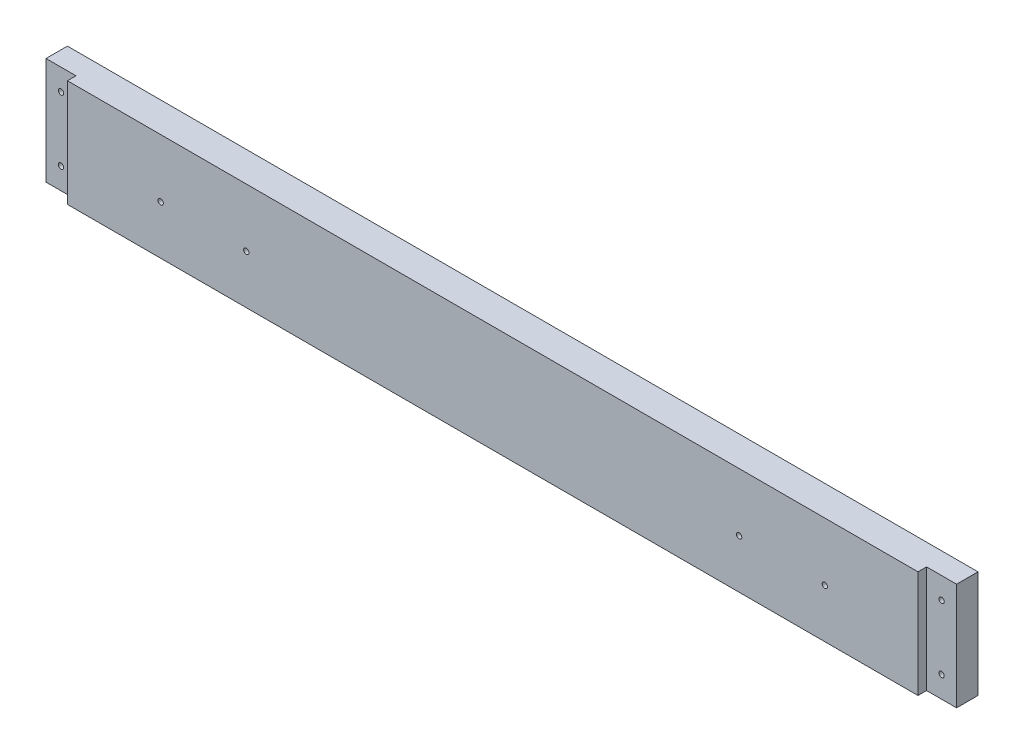
SolidWorks part; units mm, degrees
material "Pine"
ref_plane "Front Plane" through (0, 0, 0) normal (0, 0, 1) x (1, 0, 0)
ref_plane "Top Plane" through (0, 0, 0) normal (0, 1, 0) x (1, 0, 0)
ref_plane "Right Plane" through (0, 0, 0) normal (1, 0, 0) x (0, 0, -1)
sketch "Sketch1" plane through (0, 0, 0) normal (0, 0, 1) x (1, 0, 0)
  line L0 (8932.6508, -5243.5125) -> (10226.1458, -5243.5125)
  line L1 (9086.3208, -4722.0918) -> (10222.9708, -4853.7812)
  line L2 (8914.8708, -6342.0625) -> (10197.5708, -6342.0625)
  line L3 (8914.8708, -5808.6625) -> (10197.5708, -5808.6625)
  line L4 (8919.6333, -5253.0375) -> (10218.2083, -5253.0375)
  line L5 (9134.2633, -4656.1375) -> (9134.2633, -4638.3575)
  line L6 (9091.0833, -4638.3575) -> (9134.2633, -4638.3575)
  line L7 (9091.0833, -4567.2375) -> (9091.0833, -4638.3575)
  line L8 (9134.2633, -4656.1375) -> (9581.3033, -4656.1375)
  line L9 (9091.0833, -4567.2375) -> (9624.4833, -4567.2375)
  line L10 (9581.3033, -4656.1375) -> (9581.3033, -4638.3575)
  line L11 (9581.3033, -4638.3575) -> (9624.4833, -4638.3575)
  line L12 (9624.4833, -4567.2375) -> (9624.4833, -4638.3575)
  line L13 (8932.6508, -5225.7325) -> (9344.9775, -5225.7325)
  line L14 (8932.6508, -5256.2125) -> (8932.6508, -5243.5125)
  line L15 (8911.6958, -5256.2125) -> (8932.6508, -5256.2125)
  line L16 (8914.8708, -4722.0918) -> (9086.3208, -4722.0918)
  line L17 (8911.6958, -4715.5913) -> (8932.6508, -4715.5913)
  line L18 (8914.8708, -6342.0625) -> (8914.8708, -5808.6625)
  line L19 (12082.9917, -4722.0918) -> (10946.3417, -4853.7812)
  line L20 (12236.6617, -5243.5125) -> (10943.1667, -5243.5125)
  line L21 (10951.1042, -5253.0375) -> (12249.6792, -5253.0375)
  line L22 (10838.3917, -5656.2625) -> (11308.2917, -5656.2625)
  line L23 (10838.3917, -5719.7625) -> (11308.2917, -5719.7625)
  line L24 (10838.3917, -5742.5368) -> (11308.2917, -5742.5368)
  line L25 (10806.6417, -6342.0625) -> (11340.0417, -6342.0625)
  line L26 (10803.4667, -6335.7125) -> (11343.2167, -6335.7125)
  line L27 (10803.4667, -6317.9325) -> (11343.2167, -6317.9325)
  line L28 (10943.1667, -5225.7325) -> (11376.4483, -5225.7325)
  line L29 (11506.7292, -4754.5625) -> (10806.6417, -4827.5875)
  line L30 (11506.7292, -4567.2375) -> (11506.7292, -4754.5625)
  line L31 (10806.6417, -4567.2375) -> (10806.6417, -4827.5875)
  line L32 (10806.6417, -4567.2375) -> (11506.7292, -4567.2375)
  line L33 (10235.6708, -6329.3625) -> (10245.1958, -6329.3625)
  line L34 (10245.1958, -6329.3625) -> (10254.7208, -6278.5625)
  line L35 (10302.3458, -6329.3625) -> (10311.8708, -6278.5625)
  line L36 (10302.3458, -6329.3625) -> (10292.8208, -6329.3625)
  line L37 (10245.1958, -5821.3625) -> (10254.7208, -5872.1625)
  line L38 (10235.6708, -5821.3625) -> (10245.1958, -5821.3625)
  line L39 (10292.8208, -5821.3625) -> (10302.3458, -5821.3625)
  line L40 (10302.3458, -5821.3625) -> (10311.8708, -5872.1625)
  line L41 (10235.6708, -5821.3625) -> (10235.6708, -6329.3625)
  line L42 (10254.7208, -5872.1625) -> (10254.7208, -6278.5625)
  line L43 (10311.8708, -5872.1625) -> (10311.8708, -6278.5625)
  line L44 (10292.8208, -5821.3625) -> (10292.8208, -6329.3625)
  line L45 (8932.6508, -5225.7325) -> (8932.6508, -4715.5913)
  line L46 (8911.6958, -4715.5913) -> (8911.6958, -5256.2125)
  line L47 (8914.8708, -5248.275) -> (8914.8708, -4722.0918)
  line L48 (8919.6333, -5253.0375) -> (8914.8708, -5248.275)
  line L49 (8914.8708, -5145.0875) -> (8937.426, -5145.0875)
  line L50 (8914.8708, -5202.2375) -> (8937.426, -5202.2375)
  line L51 (10838.3917, -5656.2625) -> (10838.3917, -5719.7625)
  line L52 (10832.0417, -5736.1868) -> (10856.1717, -5736.1868)
  line L53 (10806.6417, -6342.0625) -> (10806.6417, -5818.7368)
  line L54 (10832.0417, -5649.9125) -> (10856.1717, -5649.9125)
  line L55 (10832.0417, -5726.1125) -> (10856.1717, -5726.1125)
  line L56 (10806.6417, -5818.7368) -> (10833.9015, -5818.7368)
  line L57 (10832.0417, -5806.0442) -> (10851.6815, -5806.0442)
  line L58 (10856.1717, -5801.5541) -> (10856.1717, -5736.1868)
  line L59 (10838.3917, -5814.2467) -> (10838.3917, -5742.5368)
  line L60 (10832.0417, -5806.0442) -> (10832.0417, -5736.1868)
  line L61 (10803.4667, -6317.9325) -> (10803.4667, -6335.7125)
  line L62 (10197.5708, -5808.6625) -> (10197.5708, -6342.0625)
  line L63 (9762.3842, -6348.4125) -> (9762.3842, -5802.3125)
  line L64 (9780.1642, -6348.4125) -> (9762.3842, -6348.4125)
  line L65 (9780.1642, -5802.3125) -> (9780.1642, -6348.4125)
  line L66 (9762.3842, -5802.3125) -> (9780.1642, -5802.3125)
  line L67 (9332.2775, -6348.4125) -> (9332.2775, -5802.3125)
  line L68 (9332.2775, -6348.4125) -> (9350.0575, -6348.4125)
  line L69 (9350.0575, -5802.3125) -> (9350.0575, -6348.4125)
  line L70 (9332.2775, -5802.3125) -> (9350.0575, -5802.3125)
  line L71 (9993.8374, -6061.075) -> (9993.8374, -6045.2418)
  line L72 (9998.5999, -6065.8375) -> (10014.4331, -6065.8375)
  line L73 (9998.5999, -6084.8875) -> (10014.4331, -6084.8875)
  line L74 (9993.8374, -6105.4832) -> (9993.8374, -6089.65)
  line L75 (9974.7874, -6105.4832) -> (9974.7874, -6089.65)
  line L76 (9954.1917, -6084.8875) -> (9970.0249, -6084.8875)
  line L77 (9974.7874, -6061.075) -> (9974.7874, -6045.2418)
  line L78 (9954.1917, -6065.8375) -> (9970.0249, -6065.8375)
  line L79 (10793.9417, -6237.2875) -> (10816.4969, -6237.2875)
  line L80 (10793.9417, -6294.4375) -> (10816.4969, -6294.4375)
  line L81 (10856.1717, -5649.9125) -> (10856.1717, -5726.1125)
  line L82 (10832.0417, -5726.1125) -> (10832.0417, -5649.9125)
  line L83 (10226.1458, -5225.7325) -> (10226.1458, -5243.5125)
  line L84 (10205.1908, -5257.8) -> (10205.1908, -4844.2499)
  line L85 (10230.9083, -4844.2499) -> (10230.9083, -5257.8)
  line L86 (10205.1908, -5257.8) -> (10230.9083, -5257.8)
  line L87 (10205.1908, -4844.2499) -> (10230.9083, -4844.2499)
  line L88 (10946.3417, -5176.8375) -> (10968.8969, -5176.8375)
  line L89 (9349.4676, -5141.9125) -> (9358.2674, -5141.9125)
  line L90 (10946.3417, -5119.6875) -> (10968.8969, -5119.6875)
  line L91 (9929.011, -4660.9635) -> (10066.0807, -4660.9635)
  line L92 (9929.011, -4678.7435) -> (10066.0807, -4678.7435)
  line L93 (10943.1667, -5225.7325) -> (10943.1667, -5243.5125)
  line L94 (10946.3417, -5248.275) -> (10951.1042, -5253.0375)
  line L95 (10946.3417, -5257.8063) -> (10946.3417, -4849.0188)
  line L96 (10964.1217, -5257.8) -> (10964.1217, -4844.2499)
  line L97 (10938.4042, -4844.2499) -> (10938.4042, -5257.8)
  line L98 (10938.4042, -5257.8) -> (10964.1217, -5257.8)
  line L99 (10964.1217, -4844.2499) -> (10938.4042, -4844.2499)
  line L100 (10344.8908, -4560.8875) -> (10369.0208, -4560.8875)
  line L101 (10344.8908, -4560.8875) -> (10369.0208, -4560.8875)
  line L102 (10800.2917, -4560.8875) -> (10824.4217, -4560.8875)
  line L103 (10200.4156, -5119.6875) -> (10222.9708, -5119.6875)
  line L104 (10200.4156, -5176.8375) -> (10222.9708, -5176.8375)
  line L105 (9344.9775, -5146.4026) -> (9344.9775, -5225.7325)
  line L106 (10344.8908, -4560.8875) -> (10344.8908, -4833.9375)
  line L107 (9792.8642, -5225.7325) -> (9792.8642, -5146.4026)
  line L108 (9362.7575, -5225.7325) -> (9775.0842, -5225.7325)
  line L109 (9680.3633, -4761.8396) -> (9680.3633, -4559.9604)
  line L110 (9656.2333, -4559.9604) -> (9680.3633, -4559.9604)
  line L111 (9656.2333, -4761.8396) -> (9680.3633, -4761.8396)
  line L112 (9656.2333, -4761.8396) -> (9656.2333, -4559.9604)
  line L113 (9779.5743, -5141.9125) -> (9788.374, -5141.9125)
  line L114 (10070.5708, -4665.4536) -> (10070.5708, -4674.2534)
  line L115 (9924.5208, -4674.2534) -> (9924.5208, -4665.4536)
  line L116 (12127.4417, -6188.3925) -> (12205.5015, -6188.3925)
  line L117 (12209.9917, -6170.6125) -> (12209.9917, -6183.9024)
  line L118 (9792.8642, -5225.7325) -> (10226.1458, -5225.7325)
  line L119 (9662.5833, -4754.5625) -> (10362.6708, -4827.5875)
  line L120 (9662.5833, -4567.2375) -> (9662.5833, -4754.5625)
  line L121 (10362.6708, -4567.2375) -> (10362.6708, -4827.5875)
  line L122 (9662.5833, -4567.2375) -> (10362.6708, -4567.2375)
  line L123 (10824.4217, -4833.9375) -> (10800.2917, -4833.9375)
  line L124 (10800.2917, -4833.9375) -> (10800.2917, -4560.8875)
  line L125 (10824.4217, -4560.8875) -> (10824.4217, -4833.9375)
  line L126 (10344.8908, -4833.9375) -> (10369.0208, -4833.9375)
  line L127 (10369.0208, -4833.9375) -> (10369.0208, -4560.8875)
  line L128 (10222.9708, -5248.275) -> (10218.2083, -5253.0375)
  line L129 (10222.9708, -5257.8063) -> (10222.9708, -4849.0188)
  line L130 (11734.6544, -5701.375) -> (11739.2301, -5701.375)
  line L131 (9362.7575, -5225.7325) -> (9362.7575, -5146.4026)
  line L132 (9775.0842, -5146.4026) -> (9775.0842, -5225.7325)
  line L133 (11761.3864, -5701.375) -> (11756.8282, -5701.375)
  line L134 (11734.6544, -5693.755) -> (11739.2301, -5693.755)
  line L135 (11761.4039, -5693.755) -> (11756.8282, -5693.755)
  line L136 (11734.6544, -5701.375) -> (11739.2301, -5701.375)
  line L137 (11744.3462, -5721.3024) -> (11744.3462, -5706.4179)
  line L138 (11751.7122, -5721.3024) -> (11751.7122, -5706.4179)
  line L139 (11740.0917, -6170.6125) -> (11740.0917, -6183.9024)
  line L140 (11689.2917, -6188.3925) -> (11822.6417, -6188.3925)
  line L141 (11689.2917, -6348.4093) -> (11689.2917, -6164.2657)
  line L142 (11689.2917, -6164.2657) -> (11746.4417, -6164.2657)
  line L143 (11746.4417, -6164.2657) -> (11746.4417, -6188.3925)
  line L144 (11689.2917, -6164.2657) -> (11746.4417, -6164.2657)
  line L145 (11340.0417, -5818.7368) -> (11340.0417, -6342.0625)
  line L146 (11290.5117, -5726.1125) -> (11314.6417, -5726.1125)
  line L147 (11290.5117, -5649.9125) -> (11290.5117, -5726.1125)
  line L148 (11340.0417, -5818.7368) -> (11312.7818, -5818.7368)
  line L149 (11314.6417, -5806.0442) -> (11295.0018, -5806.0442)
  line L150 (11290.5117, -5801.5541) -> (11290.5117, -5736.1868)
  line L151 (11308.2917, -5814.2467) -> (11308.2917, -5742.5368)
  line L152 (11314.6417, -5806.0442) -> (11314.6417, -5736.1868)
  line L153 (11290.5117, -5736.1868) -> (11314.6417, -5736.1868)
  line L154 (11848.0417, -6267.1325) -> (11962.3417, -6267.1325)
  line L155 (11962.3417, -6267.1325) -> (11962.3417, -6203.6325)
  line L156 (11343.2167, -6317.9325) -> (11343.2167, -6335.7125)
  line L157 (11365.4417, -5656.2625) -> (11365.4417, -5719.7625)
  line L158 (11365.4417, -5656.2625) -> (11479.7417, -5656.2625)
  line L159 (11778.1917, -6071.3937) -> (11802.3217, -6071.3937)
  line L160 (11314.6417, -5726.1125) -> (11314.6417, -5649.9125)
  line L161 (11314.6417, -5649.9125) -> (11290.5117, -5649.9125)
  line L162 (11308.2917, -5719.7625) -> (11308.2917, -5656.2625)
  line L163 (11689.2917, -6348.4093) -> (11713.4217, -6348.4093)
  line L164 (12203.6417, -6164.2657) -> (12260.7917, -6164.2657)
  line L165 (11713.4217, -6348.4093) -> (11713.4217, -6164.2657)
  line L166 (11695.6417, -6342.0625) -> (11695.6417, -6170.6125)
  line L167 (11695.6417, -6048.5337) -> (11699.4517, -6052.3437)
  line L168 (11822.6417, -6292.5325) -> (11822.6417, -6188.3925)
  line L169 (11695.6417, -6342.0625) -> (11695.6417, -6170.6125)
  line L170 (11848.0417, -6203.6325) -> (11962.3417, -6203.6325)
  line L171 (11848.0417, -6203.6325) -> (11848.0417, -6267.1325)
  line L172 (11987.7417, -6267.1325) -> (11987.7417, -6203.6325)
  line L173 (11784.5417, -6077.7437) -> (11784.5417, -6141.2438)
  line L174 (11517.8417, -5656.2625) -> (11632.1417, -5656.2625)
  line L175 (11632.1417, -5656.2625) -> (11632.1417, -5719.7625)
  line L176 (11632.1417, -5719.7625) -> (11517.8417, -5719.7625)
  line L177 (11517.8417, -5719.7625) -> (11517.8417, -5656.2625)
  line L178 (11692.4667, -6028.2137) -> (11692.4667, -6045.9937)
  line L179 (11695.6417, -5979.3188) -> (11718.1969, -5979.3188)
  line L180 (11695.6417, -5922.1687) -> (11718.1969, -5922.1687)
  line L181 (11821.0415, -5722.9375) -> (11821.0415, -5943.6)
  line L182 (11687.7042, -5651.5) -> (11701.9917, -5651.5)
  line L183 (11687.7042, -5651.5) -> (11687.7042, -6055.5251)
  line L184 (11687.7042, -6055.5251) -> (11701.9917, -6055.5251)
  line L185 (11701.9917, -6055.5251) -> (11701.9917, -5651.5)
  line L186 (11695.6417, -6055.2013) -> (11695.6417, -5649.595)
  line L187 (11695.6417, -5656.2625) -> (11695.6417, -6048.5337)
  line L188 (11695.6417, -6170.6125) -> (11740.0917, -6170.6125)
  line L189 (12203.6417, -6164.2657) -> (12203.6417, -6188.3925)
  line L190 (12254.4417, -6342.0625) -> (12254.4417, -6170.6125)
  line L191 (12129.0419, -5943.6) -> (12129.0419, -5722.9375)
  line L192 (12254.4417, -6048.5337) -> (12250.6317, -6052.3437)
  line L193 (12257.6167, -6045.9937) -> (12257.6167, -6028.2137)
  line L194 (12248.0917, -5651.5) -> (12262.3792, -5651.5)
  line L195 (12262.3792, -5651.5) -> (12262.3792, -6055.5251)
  line L196 (12262.3792, -6055.5251) -> (12248.0917, -6055.5251)
  line L197 (12248.0917, -6055.5251) -> (12248.0917, -5651.5)
  line L198 (12254.4417, -6141.2438) -> (12254.4417, -6077.7437)
  line L199 (12236.6617, -6164.2657) -> (12260.7917, -6164.2657)
  line L200 (12102.0417, -6267.1325) -> (11987.7417, -6267.1325)
  line L201 (11330.1865, -6237.2875) -> (11352.7417, -6237.2875)
  line L202 (11330.1865, -6294.4375) -> (11352.7417, -6294.4375)
  line L203 (11474.6617, -5851.8425) -> (11492.4417, -5851.8425)
  line L204 (11474.6617, -5808.6625) -> (11474.6617, -5851.8425)
  line L205 (11403.5417, -5808.6625) -> (11474.6617, -5808.6625)
  line L206 (11492.4417, -5851.8425) -> (11492.4417, -6298.8825)
  line L207 (11403.5417, -6342.0625) -> (11403.5417, -5808.6625)
  line L208 (11474.6617, -6298.8825) -> (11492.4417, -6298.8825)
  line L209 (11474.6617, -6342.0625) -> (11474.6617, -6298.8825)
  line L210 (11403.5417, -6342.0625) -> (11474.6617, -6342.0625)
  line L211 (11619.4417, -5851.8425) -> (11601.6617, -5851.8425)
  line L212 (11601.6617, -5808.6625) -> (11601.6617, -5851.8425)
  line L213 (11530.5417, -5808.6625) -> (11601.6617, -5808.6625)
  line L214 (11619.4417, -5851.8425) -> (11619.4417, -6298.8825)
  line L215 (11530.5417, -6342.0625) -> (11530.5417, -5808.6625)
  line L216 (11619.4417, -6298.8825) -> (11601.6617, -6298.8825)
  line L217 (11601.6617, -6342.0625) -> (11601.6617, -6298.8825)
  line L218 (11530.5417, -6342.0625) -> (11601.6617, -6342.0625)
  line L219 (11479.7417, -5719.7625) -> (11479.7417, -5656.2625)
  line L220 (11365.4417, -5719.7625) -> (11479.7417, -5719.7625)
  line L221 (11778.1917, -6147.5937) -> (11802.3217, -6147.5937)
  line L222 (11802.3217, -6071.3937) -> (11802.3217, -6147.5937)
  line L223 (11778.1917, -6147.5937) -> (11778.1917, -6071.3937)
  line L224 (12254.4417, -5922.1687) -> (12231.8865, -5922.1687)
  line L225 (12254.4417, -5979.3188) -> (12231.8865, -5979.3188)
  line L226 (12254.4417, -6055.2013) -> (12254.4417, -5649.595)
  line L227 (12254.4417, -6048.5337) -> (12254.4417, -5656.2625)
  line L228 (11841.6917, -5702.2873) -> (12108.3917, -5702.2873)
  line L229 (11822.6417, -6292.5325) -> (12127.4417, -6292.5325)
  line L230 (12127.4417, -6292.5325) -> (12127.4417, -6188.3925)
  line L231 (12254.4417, -6170.6125) -> (12209.9917, -6170.6125)
  line L232 (11695.6417, -6342.0625) -> (12254.4417, -6342.0625)
  line L233 (12236.6617, -6348.4093) -> (12260.7917, -6348.4093)
  line L234 (12260.7917, -6348.4093) -> (12260.7917, -6164.2657)
  line L235 (12236.6617, -6348.4093) -> (12236.6617, -6164.2657)
  line L236 (12102.0417, -6203.6325) -> (12102.0417, -6267.1325)
  line L237 (11987.7417, -6203.6325) -> (12102.0417, -6203.6325)
  line L238 (12236.6617, -6147.5937) -> (12236.6617, -6071.3937)
  line L239 (12203.6417, -6188.3925) -> (12260.7917, -6188.3925)
  line L240 (11098.7417, -4665.4536) -> (11098.7417, -4674.2534)
  line L241 (11394.2283, -5146.4026) -> (11394.2283, -5225.7325)
  line L242 (11376.4483, -5225.7325) -> (11376.4483, -5146.4026)
  line L243 (11394.2283, -5225.7325) -> (11806.555, -5225.7325)
  line L244 (11841.6917, -5964.2502) -> (12108.3917, -5964.2502)
  line L245 (12236.6617, -6147.5937) -> (12260.7917, -6147.5937)
  line L246 (12236.6617, -5256.2125) -> (12236.6617, -5243.5125)
  line L247 (12260.7917, -6147.5937) -> (12260.7917, -6071.3937)
  line L248 (12260.7917, -6071.3937) -> (12236.6617, -6071.3937)
  line L249 (12254.4417, -6077.7437) -> (11784.5417, -6077.7437)
  line L250 (11784.5417, -6141.2438) -> (12254.4417, -6141.2438)
  line L252 (12254.4417, -5656.2625) -> (11695.6417, -5656.2625)
  line L253 (11699.4517, -6052.3437) -> (12250.6317, -6052.3437)
  line L254 (11692.4667, -6045.9937) -> (12257.6167, -6045.9937)
  line L255 (11692.4667, -6028.2137) -> (12257.6167, -6028.2137)
  line L256 (11824.335, -5146.4026) -> (11824.335, -5225.7325)
  line L257 (11811.0451, -5141.9125) -> (11819.8449, -5141.9125)
  line L258 (11244.7917, -4674.2534) -> (11244.7917, -4665.4536)
  line L259 (11806.555, -5225.7325) -> (11806.555, -5146.4026)
  line L260 (11488.9492, -4761.8396) -> (11488.9492, -4559.9604)
  line L261 (11488.9492, -4559.9604) -> (11513.0792, -4559.9604)
  line L262 (11488.9492, -4761.8396) -> (11513.0792, -4761.8396)
  line L263 (11513.0792, -4761.8396) -> (11513.0792, -4559.9604)
  line L264 (11240.3015, -4660.9635) -> (11103.2318, -4660.9635)
  line L265 (11103.2318, -4678.7435) -> (11240.3015, -4678.7435)
  line L266 (12236.6617, -5225.7325) -> (12236.6617, -4715.5913)
  line L267 (12257.6167, -4715.5913) -> (12257.6167, -5256.2125)
  line L268 (12254.4417, -5248.275) -> (12254.4417, -4722.0918)
  line L269 (12236.6617, -5225.7325) -> (11824.335, -5225.7325)
  line L270 (12035.0492, -4656.1375) -> (12035.0492, -4638.3575)
  line L271 (12078.2292, -4638.3575) -> (12035.0492, -4638.3575)
  line L272 (12078.2292, -4567.2375) -> (12078.2292, -4638.3575)
  line L273 (12035.0492, -4656.1375) -> (11588.0092, -4656.1375)
  line L274 (11544.8292, -4567.2375) -> (12078.2292, -4567.2375)
  line L275 (11588.0092, -4656.1375) -> (11588.0092, -4638.3575)
  line L276 (11544.8292, -4638.3575) -> (11588.0092, -4638.3575)
  line L277 (11544.8292, -4567.2375) -> (11544.8292, -4638.3575)
  line L278 (12249.6792, -5253.0375) -> (12254.4417, -5248.275)
  line L280 (12257.6167, -5256.2125) -> (12236.6617, -5256.2125)
  line L281 (12231.8865, -5145.0875) -> (12254.4417, -5145.0875)
  line L282 (12231.8865, -5202.2375) -> (12254.4417, -5202.2375)
  line L283 (12236.6617, -4715.5913) -> (12257.6167, -4715.5913)
  line L284 (12082.9917, -4722.0918) -> (12254.4417, -4722.0918)
  line L285 (11380.9385, -5141.9125) -> (11389.7382, -5141.9125)
  circle A0 centre (8923.7608, -4778.9042) radius 1.5875
  circle A1 centre (9062.6598, -4736.3765) radius 2.3685
  circle A2 centre (9051.3958, -6281.7375) radius 22.225
  circle A3 centre (9083.1458, -6249.9875) radius 1.5875
  circle A4 centre (9083.1458, -6313.4875) radius 1.5875
  circle A5 centre (9019.6458, -6249.9875) radius 1.5875
  circle A6 centre (9019.6458, -6313.4875) radius 1.5875
  circle A7 centre (8972.3383, -5202.2375) radius 1.5875
  circle A8 centre (8923.7608, -5015.9708) radius 1.5875
  circle A9 centre (8923.7608, -5134.5042) radius 1.5875
  circle A10 centre (9054.5708, -5234.6225) radius 1.5875
  circle A11 centre (8923.7608, -4897.4375) radius 1.5875
  circle A12 centre (8972.3383, -5087.9375) radius 1.5875
  circle A13 centre (8972.3383, -5145.0875) radius 1.5875
  circle A14 centre (10847.2817, -5668.9625) radius 1.5875
  circle A15 centre (10847.2817, -5707.0625) radius 1.5875
  circle A16 centre (10847.2817, -5755.2368) radius 1.5875
  circle A17 centre (10851.4092, -6237.2875) radius 1.5875
  circle A18 centre (10851.4092, -6294.4375) radius 1.5875
  circle A19 centre (10847.2817, -5793.3442) radius 1.5875
  arc A20 (10833.9015, -5818.7368) -> (10838.3917, -5814.2467) centre (10836.1466, -5816.4918) ccw
  arc A21 (10851.6815, -5806.0442) -> (10856.1717, -5801.5541) centre (10853.9266, -5803.7992) ccw
  circle A22 centre (10882.8417, -6040.4375) radius 1.5875
  circle A23 centre (10882.8417, -6218.2375) radius 1.5875
  circle A24 centre (10882.8417, -5862.6375) radius 1.5875
  circle A25 centre (10908.2417, -6326.8225) radius 1.5875
  circle A26 centre (10908.2417, -6326.8225) radius 1.5875
  circle A27 centre (10851.4092, -6180.1375) radius 1.5875
  circle A28 centre (10815.5317, -4783.4231) radius 1.5875
  circle A29 centre (10815.5317, -4696.9488) radius 1.5875
  circle A30 centre (10815.5317, -4610.4746) radius 1.5875
  circle A31 centre (10979.1323, -4867.0082) radius 2.3685
  circle A32 centre (10190.1802, -4867.0082) radius 2.3685
  circle A33 centre (10955.2317, -4929.9812) radius 1.5875
  circle A34 centre (10955.2317, -5031.5812) radius 1.5875
  circle A35 centre (10214.0808, -4929.9812) radius 1.5875
  circle A36 centre (10214.0808, -5031.5812) radius 1.5875
  circle A37 centre (9341.1675, -6265.8625) radius 1.5875
  circle A38 centre (9771.2742, -5884.8625) radius 1.5875
  circle A39 centre (9771.2742, -6138.8625) radius 1.5875
  circle A40 centre (9771.2742, -6011.8625) radius 1.5875
  arc A41 (10036.2287, -6113.8083) -> (10051.3426, -6111.6033) centre (10042.9639, -6107.0732) ccw
  arc A42 (10051.3426, -6111.6033) -> (10051.3426, -6039.1217) centre (9984.3124, -6075.3625) ccw
  arc A43 (10051.3426, -6039.1217) -> (10036.2287, -6036.9167) centre (10042.9639, -6043.6518) ccw
  arc A44 (10034.5851, -6102.5431) -> (10034.5851, -6048.1819) centre (9984.3124, -6075.3625) ccw
  arc A45 (10034.5851, -6102.5431) -> (10036.2287, -6113.8083) centre (10042.9639, -6107.0732) ccw
  arc A46 (10036.2287, -6036.9167) -> (10034.5851, -6048.1819) centre (10042.9639, -6043.6518) ccw
  arc A47 (9945.8666, -6127.2787) -> (9948.0717, -6142.3927) centre (9952.6018, -6134.0139) ccw
  arc A48 (9948.0717, -6142.3927) -> (10020.5532, -6142.3927) centre (9984.3124, -6075.3625) ccw
  arc A49 (10020.5532, -6142.3927) -> (10022.7583, -6127.2787) centre (10016.0231, -6134.0139) ccw
  arc A50 (9957.1319, -6125.6352) -> (10011.493, -6125.6352) centre (9984.3124, -6075.3625) ccw
  arc A51 (9957.1319, -6125.6352) -> (9945.8666, -6127.2787) centre (9952.6018, -6134.0139) ccw
  arc A52 (10022.7583, -6127.2787) -> (10011.493, -6125.6352) centre (10016.0231, -6134.0139) ccw
  arc A53 (9932.3962, -6036.9167) -> (9917.2822, -6039.1217) centre (9925.661, -6043.6518) ccw
  arc A54 (9917.2822, -6039.1217) -> (9917.2822, -6111.6033) centre (9984.3124, -6075.3625) ccw
  arc A55 (9917.2822, -6111.6033) -> (9932.3962, -6113.8083) centre (9925.661, -6107.0732) ccw
  arc A56 (9934.0398, -6048.1819) -> (9934.0398, -6102.5431) centre (9984.3124, -6075.3625) ccw
  arc A57 (9934.0398, -6048.1819) -> (9932.3962, -6036.9167) centre (9925.661, -6043.6518) ccw
  arc A58 (9932.3962, -6113.8083) -> (9934.0398, -6102.5431) centre (9925.661, -6107.0732) ccw
  arc A59 (9945.8666, -6023.4463) -> (9957.1319, -6025.0898) centre (9952.6018, -6016.7111) ccw
  arc A60 (10011.493, -6025.0898) -> (10022.7583, -6023.4463) centre (10016.0231, -6016.7111) ccw
  arc A61 (10011.493, -6025.0898) -> (9957.1319, -6025.0898) centre (9984.3124, -6075.3625) ccw
  arc A62 (9948.0717, -6008.3323) -> (9945.8666, -6023.4463) centre (9952.6018, -6016.7111) ccw
  arc A63 (10020.5532, -6008.3323) -> (9948.0717, -6008.3323) centre (9984.3124, -6075.3625) ccw
  arc A64 (10022.7583, -6023.4463) -> (10020.5532, -6008.3323) centre (10016.0231, -6016.7111) ccw
  arc A65 (10005.0943, -6187.7574) -> (10096.7073, -6096.1443) centre (9984.3124, -6075.3625) ccw
  arc A66 (9993.8374, -6178.3911) -> (10005.0943, -6187.7574) centre (10003.3624, -6178.3911) ccw
  arc A67 (10001.6306, -6169.0249) -> (10077.9748, -6092.6807) centre (9984.3124, -6075.3625) ccw
  arc A68 (10087.3411, -6084.8875) -> (10077.9748, -6092.6807) centre (10087.3411, -6094.4125) ccw
  arc A69 (10001.6306, -6169.0249) -> (9993.8374, -6178.3911) centre (10003.3624, -6178.3911) ccw
  arc A70 (9963.5306, -6187.7574) -> (9974.7874, -6178.3911) centre (9965.2624, -6178.3911) ccw
  arc A71 (9871.9176, -6096.1443) -> (9963.5306, -6187.7574) centre (9984.3124, -6075.3625) ccw
  arc A72 (9881.2838, -6084.8875) -> (9871.9176, -6096.1443) centre (9881.2838, -6094.4125) ccw
  arc A73 (9890.65, -6092.6807) -> (9966.9943, -6169.0249) centre (9984.3124, -6075.3625) ccw
  arc A74 (9974.7874, -6178.3911) -> (9966.9943, -6169.0249) centre (9965.2624, -6178.3911) ccw
  arc A75 (9890.65, -6092.6807) -> (9881.2838, -6084.8875) centre (9881.2838, -6094.4125) ccw
  arc A76 (9871.9176, -6054.5807) -> (9881.2838, -6065.8375) centre (9881.2838, -6056.3125) ccw
  arc A77 (9963.5306, -5962.9676) -> (9871.9176, -6054.5807) centre (9984.3124, -6075.3625) ccw
  arc A78 (9974.7874, -5972.3339) -> (9963.5306, -5962.9676) centre (9965.2624, -5972.3339) ccw
  arc A79 (9966.9943, -5981.7001) -> (9890.65, -6058.0443) centre (9984.3124, -6075.3625) ccw
  arc A80 (9881.2838, -6065.8375) -> (9890.65, -6058.0443) centre (9881.2838, -6056.3125) ccw
  arc A81 (9966.9943, -5981.7001) -> (9974.7874, -5972.3339) centre (9965.2624, -5972.3339) ccw
  arc A82 (10077.9748, -6058.0443) -> (10087.3411, -6065.8375) centre (10087.3411, -6056.3125) ccw
  arc A83 (9993.8374, -5972.3339) -> (10001.6306, -5981.7001) centre (10003.3624, -5972.3339) ccw
  arc A84 (10077.9748, -6058.0443) -> (10001.6306, -5981.7001) centre (9984.3124, -6075.3625) ccw
  arc A85 (10087.3411, -6065.8375) -> (10096.7073, -6054.5807) centre (10087.3411, -6056.3125) ccw
  arc A86 (10096.7073, -6054.5807) -> (10005.0943, -5962.9676) centre (9984.3124, -6075.3625) ccw
  arc A87 (10005.0943, -5962.9676) -> (9993.8374, -5972.3339) centre (10003.3624, -5972.3339) ccw
  arc A88 (10014.4331, -6065.8375) -> (10018.7361, -6059.0339) centre (10014.4331, -6061.075) ccw
  arc A89 (10018.7361, -6059.0339) -> (10000.641, -6040.9388) centre (9984.3124, -6075.3625) ccw
  arc A90 (10000.641, -6040.9388) -> (9993.8374, -6045.2418) centre (9998.5999, -6045.2418) ccw
  arc A91 (9993.8374, -6061.075) -> (9998.5999, -6065.8375) centre (9998.5999, -6061.075) ccw
  arc A92 (9993.8374, -6105.4832) -> (10000.641, -6109.7862) centre (9998.5999, -6105.4832) ccw
  arc A93 (10000.641, -6109.7862) -> (10018.7361, -6091.6911) centre (9984.3124, -6075.3625) ccw
  arc A94 (10018.7361, -6091.6911) -> (10014.4331, -6084.8875) centre (10014.4331, -6089.65) ccw
  arc A95 (9998.5999, -6084.8875) -> (9993.8374, -6089.65) centre (9998.5999, -6089.65) ccw
  arc A96 (9954.1917, -6084.8875) -> (9949.8888, -6091.6911) centre (9954.1917, -6089.65) ccw
  arc A97 (9949.8888, -6091.6911) -> (9967.9839, -6109.7862) centre (9984.3124, -6075.3625) ccw
  arc A98 (9967.9839, -6109.7862) -> (9974.7874, -6105.4832) centre (9970.0249, -6105.4832) ccw
  arc A99 (9974.7874, -6089.65) -> (9970.0249, -6084.8875) centre (9970.0249, -6089.65) ccw
  arc A100 (9970.0249, -6065.8375) -> (9974.7874, -6061.075) centre (9970.0249, -6061.075) ccw
  arc A101 (9949.8888, -6059.0339) -> (9954.1917, -6065.8375) centre (9954.1917, -6061.075) ccw
  arc A102 (9967.9839, -6040.9388) -> (9949.8888, -6059.0339) centre (9984.3124, -6075.3625) ccw
  arc A103 (9974.7874, -6045.2418) -> (9967.9839, -6040.9388) centre (9970.0249, -6045.2418) ccw
  arc A104 (10096.7073, -6096.1443) -> (10087.3411, -6084.8875) centre (10087.3411, -6094.4125) ccw
  circle A105 centre (9771.2742, -6265.8625) radius 1.5875
  circle A106 centre (9341.1675, -5884.8625) radius 1.5875
  circle A107 centre (9341.1675, -6138.8625) radius 1.5875
  circle A108 centre (9341.1675, -6011.8625) radius 1.5875
  circle A109 centre (11037.2315, -4887.5494) radius 15.0812
  arc A110 (9349.4676, -5141.9125) -> (9344.9775, -5146.4026) centre (9347.2226, -5144.1576) ccw
  arc A111 (9362.7575, -5146.4026) -> (9358.2674, -5141.9125) centre (9360.5124, -5144.1576) ccw
  circle A112 centre (9946.7458, -4669.8535) radius 1.5875
  arc A113 (9924.5208, -4674.2534) -> (9929.011, -4678.7435) centre (9926.7659, -4676.4984) ccw
  circle A114 centre (11003.8092, -5176.8375) radius 1.5875
  circle A115 centre (11003.8092, -5119.6875) radius 1.5875
  circle A116 centre (10353.7808, -4696.9488) radius 1.5875
  circle A117 centre (10353.7808, -4610.4746) radius 1.5875
  circle A118 centre (10353.7808, -4783.4231) radius 1.5875
  circle A119 centre (11003.8092, -5062.5375) radius 1.5875
  circle A120 centre (9353.8675, -5160.9625) radius 1.5875
  circle A121 centre (9638.7708, -5234.6225) radius 1.5875
  circle A122 centre (9671.4733, -4724.1144) radius 1.5875
  circle A123 centre (9671.4733, -4661.3637) radius 1.5875
  circle A124 centre (9671.4733, -4598.6129) radius 1.5875
  arc A125 (9792.8642, -5146.4026) -> (9788.374, -5141.9125) centre (9790.6191, -5144.1576) ccw
  arc A126 (9779.5743, -5141.9125) -> (9775.0842, -5146.4026) centre (9777.3292, -5144.1576) ccw
  circle A127 centre (10048.3458, -4669.8535) radius 1.5875
  arc A128 (10070.5708, -4665.4536) -> (10066.0807, -4660.9635) centre (10068.3258, -4663.2086) ccw
  arc A129 (10066.0807, -4678.7435) -> (10070.5708, -4674.2534) centre (10068.3258, -4676.4984) ccw
  circle A130 centre (9997.5458, -4669.8535) radius 1.5875
  arc A131 (9929.011, -4660.9635) -> (9924.5208, -4665.4536) centre (9926.7659, -4663.2086) ccw
  circle A132 centre (10132.081, -4887.5494) radius 15.0812
  circle A133 centre (10165.5033, -5176.8375) radius 1.5875
  circle A134 centre (10165.5033, -5119.6875) radius 1.5875
  circle A135 centre (9486.3708, -5234.6225) radius 1.5875
  circle A136 centre (10165.5033, -5062.5375) radius 1.5875
  circle A137 centre (9206.9708, -5234.6225) radius 1.5875
  circle A138 centre (10070.5708, -5234.6225) radius 1.5875
  circle A139 centre (9918.1708, -5234.6225) radius 1.5875
  circle A140 centre (9783.9742, -5160.9625) radius 1.5875
  circle A141 centre (9783.9742, -5193.9825) radius 1.5875
  circle A142 centre (9353.8675, -5193.9825) radius 1.5875
  circle A143 centre (11073.3417, -6326.8225) radius 1.5875
  circle A144 centre (11073.3417, -6326.8225) radius 1.5875
  circle A145 centre (11295.2742, -6180.1375) radius 1.5875
  circle A146 centre (11295.2742, -6294.4375) radius 1.5875
  circle A147 centre (11295.2742, -6237.2875) radius 1.5875
  circle A148 centre (11975.0417, -5692.775) radius 3.4925
  circle A149 centre (11263.8417, -5862.6375) radius 1.5875
  arc A150 (11739.2301, -5701.375) -> (11744.3462, -5706.4179) centre (11748.0292, -5697.565) ccw
  arc A151 (11751.7122, -5706.4179) -> (11756.8282, -5701.375) centre (11748.0292, -5697.565) ccw
  arc A152 (11744.3462, -5721.3024) -> (11751.7122, -5721.3024) centre (11748.0292, -5725.505) ccw
  arc A153 (11734.6544, -5693.755) -> (11724.9787, -5697.565) centre (11730.5667, -5697.565) ccw
  arc A154 (11756.8282, -5693.755) -> (11739.2301, -5693.755) centre (11748.0292, -5697.565) ccw
  arc A155 (11724.9787, -5697.565) -> (11734.6544, -5701.375) centre (11730.5667, -5697.565) ccw
  arc A156 (11761.3864, -5701.375) -> (11771.0797, -5697.565) centre (11765.4842, -5697.565) ccw
  arc A157 (11771.0797, -5697.565) -> (11761.4039, -5693.755) centre (11765.4917, -5697.565) ccw
  arc A158 (11740.0917, -6183.9024) -> (11744.5818, -6188.3925) centre (11742.3367, -6186.1474) ccw
  arc A159 (12205.5015, -6188.3925) -> (12209.9917, -6183.9024) centre (12207.7466, -6186.1474) ccw
  circle A160 centre (11299.4017, -5793.3442) radius 1.5875
  arc A161 (11308.2917, -5814.2467) -> (11312.7818, -5818.7368) centre (11310.5367, -5816.4918) ccw
  arc A162 (11290.5117, -5801.5541) -> (11295.0018, -5806.0442) centre (11292.7567, -5803.7992) ccw
  circle A163 centre (11704.5317, -6314.149) radius 1.5875
  circle A164 centre (11748.9817, -6208.7125) radius 1.5875
  circle A165 centre (11263.8417, -6218.2375) radius 1.5875
  circle A166 centre (11263.8417, -6040.4375) radius 1.5875
  circle A167 centre (11238.4417, -6326.8225) radius 1.5875
  circle A168 centre (11238.4417, -6326.8225) radius 1.5875
  circle A169 centre (11299.4017, -5668.9625) radius 1.5875
  circle A170 centre (11299.4017, -5707.0625) radius 1.5875
  circle A171 centre (11726.7567, -6179.5025) radius 1.5875
  circle A172 centre (11704.5317, -6199.3198) radius 1.5875
  circle A173 centre (11748.9817, -6272.2125) radius 1.5875
  circle A174 centre (11704.5317, -6256.7344) radius 1.5875
  circle A175 centre (11299.4017, -5755.2368) radius 1.5875
  circle A176 centre (11913.4467, -6301.4225) radius 1.5875
  circle A177 centre (11790.2567, -6301.4225) radius 1.5875
  circle A178 centre (11793.4317, -6128.5437) radius 1.5875
  circle A179 centre (11753.1092, -5865.0188) radius 1.5875
  circle A180 centre (11809.9417, -6037.1038) radius 1.5875
  circle A181 centre (11809.9417, -6037.1038) radius 1.5875
  circle A182 centre (11753.1092, -5922.1687) radius 1.5875
  circle A183 centre (11975.0417, -5973.7625) radius 3.4925
  circle A184 centre (11975.0417, -6037.1038) radius 1.5875
  circle A185 centre (11753.1092, -5979.3188) radius 1.5875
  circle A186 centre (11975.0417, -6037.1038) radius 1.5875
  arc A187 (11841.6917, -5702.2873) -> (11821.0415, -5722.9375) centre (11841.6917, -5722.9375) ccw
  circle A188 centre (11811.5292, -5833.2687) radius 3.4925
  arc A189 (11821.0415, -5943.6) -> (11841.6917, -5964.2502) centre (11841.6917, -5943.6) ccw
  circle A190 centre (12196.9742, -5865.0188) radius 1.5875
  arc A191 (12129.0419, -5722.9375) -> (12108.3917, -5702.2873) centre (12108.3917, -5722.9375) ccw
  circle A192 centre (12036.6367, -6301.4225) radius 1.5875
  circle A193 centre (12159.8267, -6301.4225) radius 1.5875
  circle A194 centre (12138.5542, -5833.2687) radius 3.4925
  circle A195 centre (12197.2917, -5761.0375) radius 15.0812
  circle A196 centre (11793.4317, -6090.4437) radius 1.5875
  circle A197 centre (12196.9742, -5922.1687) radius 1.5875
  arc A198 (12108.3917, -5964.2502) -> (12129.0419, -5943.6) centre (12108.3917, -5943.6) ccw
  circle A199 centre (12196.9742, -5979.3188) radius 1.5875
  circle A200 centre (12201.1017, -6272.2125) radius 1.5875
  circle A201 centre (12245.5517, -6314.149) radius 1.5875
  circle A202 centre (12245.5517, -6256.7344) radius 1.5875
  circle A203 centre (12201.1017, -6208.7125) radius 1.5875
  circle A204 centre (12223.3267, -6179.5025) radius 1.5875
  circle A205 centre (12245.5517, -6199.3198) radius 1.5875
  circle A206 centre (11171.7667, -4669.8535) radius 1.5875
  circle A207 centre (11222.5667, -4669.8535) radius 1.5875
  arc A208 (11240.3015, -4678.7435) -> (11244.7917, -4674.2534) centre (11242.5466, -4676.4984) ccw
  circle A209 centre (11385.3383, -5193.9825) radius 1.5875
  circle A210 centre (12106.6527, -4736.3765) radius 2.3685
  circle A211 centre (12140.1417, -6037.1038) radius 1.5875
  circle A212 centre (12140.1417, -6037.1038) radius 1.5875
  circle A213 centre (12245.5517, -6090.4437) radius 1.5875
  circle A214 centre (12245.5517, -6128.5437) radius 1.5875
  circle A215 centre (11385.3383, -5160.9625) radius 1.5875
  arc A216 (11824.335, -5146.4026) -> (11819.8449, -5141.9125) centre (11822.0899, -5144.1576) ccw
  arc A217 (11811.0451, -5141.9125) -> (11806.555, -5146.4026) centre (11808.8001, -5144.1576) ccw
  circle A218 centre (11815.445, -5193.9825) radius 1.5875
  circle A219 centre (11815.445, -5160.9625) radius 1.5875
  circle A220 centre (11530.5417, -5234.6225) radius 1.5875
  circle A221 centre (11962.3417, -5234.6225) radius 1.5875
  arc A222 (11244.7917, -4665.4536) -> (11240.3015, -4660.9635) centre (11242.5466, -4663.2086) ccw
  circle A223 centre (11682.9417, -5234.6225) radius 1.5875
  circle A224 centre (11497.8392, -4724.1144) radius 1.5875
  circle A225 centre (11497.8392, -4661.3637) radius 1.5875
  circle A226 centre (11497.8392, -4598.6129) radius 1.5875
  circle A227 centre (11120.9667, -4669.8535) radius 1.5875
  arc A228 (11103.2318, -4660.9635) -> (11098.7417, -4665.4536) centre (11100.9867, -4663.2086) ccw
  arc A229 (11098.7417, -4674.2534) -> (11103.2318, -4678.7435) centre (11100.9867, -4676.4984) ccw
  circle A230 centre (12196.9742, -5202.2375) radius 1.5875
  circle A231 centre (12245.5517, -5015.9708) radius 1.5875
  circle A232 centre (12245.5517, -5134.5042) radius 1.5875
  circle A233 centre (12114.7417, -5234.6225) radius 1.5875
  circle A234 centre (12245.5517, -4897.4375) radius 1.5875
  circle A235 centre (12245.5517, -4778.9042) radius 1.5875
  circle A236 centre (12196.9742, -5087.9375) radius 1.5875
  circle A237 centre (12196.9742, -5145.0875) radius 1.5875
  circle A238 centre (11098.7417, -5234.6225) radius 1.5875
  circle A239 centre (11251.1417, -5234.6225) radius 1.5875
  arc A240 (11380.9385, -5141.9125) -> (11376.4483, -5146.4026) centre (11378.6934, -5144.1576) ccw
  arc A241 (11394.2283, -5146.4026) -> (11389.7382, -5141.9125) centre (11391.9833, -5144.1576) ccw
sketch "PedOutline" plane through (0, 0, 0) normal (0, 0, 1) x (1, 0, 0)
  line L0 (11378.1417, -5719.7625) -> (11378.1417, -5656.2625)
  line L1 (11378.1417, -5656.2625) -> (10838.3917, -5656.2625)
  line L2 (10838.3917, -5656.2625) -> (10838.3917, -5719.7625)
  line L3 (10838.3917, -5719.7625) -> (11378.1417, -5719.7625)
  dimension "Ped_Height" = 63.5
  dimension "Ped_Width" = 539.75
extrude "PedOutline_Thickness" add sketch "PedOutline" against normal blind 17.78
sketch "PedLedgeCuts" plane through (0, 0, 0) normal (0, 0, 1) x (1, 0, 0)
  line L0 (11360.3617, -5656.2625) -> (11378.1417, -5656.2625)
  line L1 (11378.1417, -5656.2625) -> (11378.1417, -5719.7625)
  line L2 (11378.1417, -5719.7625) -> (11360.3617, -5719.7625)
  line L3 (11360.3617, -5719.7625) -> (11360.3617, -5656.2625)
  line L4 (10856.1717, -5656.2625) -> (10856.1717, -5719.7625)
  line L5 (10856.1717, -5719.7625) -> (10838.3917, -5719.7625)
  line L6 (10838.3917, -5719.7625) -> (10838.3917, -5656.2625)
  line L7 (10838.3917, -5656.2625) -> (10856.1717, -5656.2625)
  line L8 (10838.3917, -5719.7625) -> (11378.1417, -5719.7625) construction
  line L9 (11378.1417, -5656.2625) -> (10838.3917, -5656.2625) construction
  dimension "Ped_Thickness" = 17.78
  dimension "Ped_Thickness2" = 17.78
extrude "PedLedgeCuts_Depth" cut sketch "PedLedgeCuts" against normal blind 5.08
sketch "Sketch4" plane through (0, 0, 0) normal (0, 0, 1) x (1, 0, 0)
  line L0 (10838.3917, -5688.0125) -> (10856.1717, -5688.0125) construction
  line L1 (10838.3917, -5656.2625) -> (10838.3917, -5719.7625) construction
  line L2 (10856.1717, -5719.7625) -> (10856.1717, -5656.2625) construction
  line L3 (11378.1417, -5688.0125) -> (11360.3617, -5688.0125) construction
  line L4 (10847.2817, -5688.0125) -> (10847.2817, -5668.9625) construction
  line L5 (10847.2817, -5688.0125) -> (10847.2817, -5707.0625) construction
  line L6 (11378.1417, -5719.7625) -> (11378.1417, -5656.2625) construction
  line L7 (11360.3617, -5656.2625) -> (11360.3617, -5719.7625) construction
  line L8 (11369.2517, -5688.0125) -> (11369.2517, -5668.9625) construction
  line L9 (11369.2517, -5688.0125) -> (11369.2517, -5707.0625) construction
  circle A0 centre (10847.2817, -5668.9625) radius 1.5875
  circle A1 centre (10847.2817, -5707.0625) radius 1.5875
  circle A2 centre (11369.2517, -5707.0625) radius 1.5875
  circle A3 centre (11369.2517, -5668.9625) radius 1.5875
  dimension "D1" = 38.1
  dimension "D2" = 38.1
extrude "Cut-Extrude2" cut sketch "Sketch4" against normal up to surface (17.78 mm away) up to face at (11108.2667, -5688.0125, -17.78)
sketch "Sketch5" plane through (0, 0, -17.78) normal (0, 0, -1) x (-1, 0, 0)
  circle A0 centre (-10911.4167, -5690.7874) radius 1.5875
  circle A1 centre (-10962.2167, -5690.7874) radius 1.5875
  circle A2 centre (-11254.3167, -5690.7874) radius 1.5875
  circle A3 centre (-11305.1167, -5690.7874) radius 1.5875
extrude "Cut-Extrude3" cut sketch "Sketch5" against normal up to surface (17.78 mm away) up to face at (11108.2667, -5688.0125, 0)
